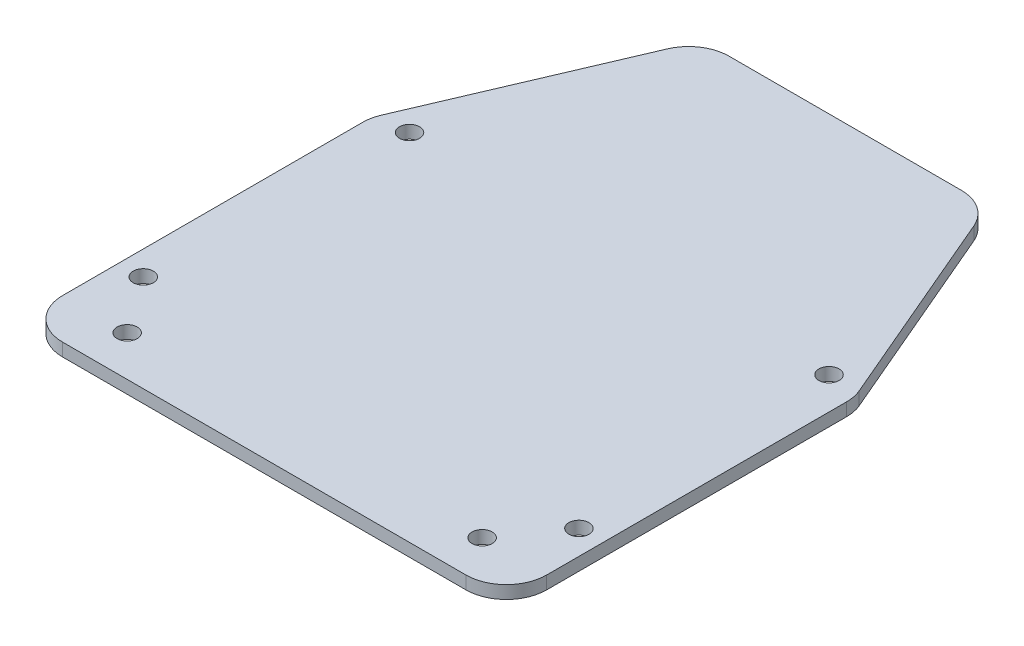
SolidWorks part; units mm, degrees
ref_plane "Front Plane" through (0, 0, 0) normal (0, 0, 1) x (1, 0, 0)
ref_plane "Top Plane" through (0, 0, 0) normal (0, 1, 0) x (1, 0, 0)
ref_plane "Right Plane" through (0, 0, 0) normal (1, 0, 0) x (0, 0, -1)
sketch "Sketch1" plane through (0, 0, 0) normal (0, 1, 0) x (1, 0, 0)
  line L0 (-17.7, 36) -> (-30, 7.2)
  line L1 (-30, -36) -> (30, -36)
  line L2 (-30, -36) -> (-30, 36)
  line L3 (-30, 36) -> (30, 36)
  line L4 (30, -36) -> (30, 36)
  line L5 (-30, -36) -> (30, 36) construction
  line L6 (-30, 36) -> (30, -36) construction
  line L7 (0, 0) -> (0, 36) construction
  line L8 (17.7, 36) -> (30, 7.2)
  point P0 (0, 0)
  dimension "D1" = 72
  dimension "D2" = 60
  dimension "D3" = 12.3
  dimension "D4" = 28.8
extrude "Boss-Extrude1" add sketch "Sketch1" along normal blind 1.6 contours L8 L3 L0 L2 L1 L4
sketch "Sketch2" plane through (0, 0, 0) normal (0, 1, 0) x (1, 0, 0)
  line L0 (30, -36) -> (30, 7.2) construction
  line L1 (-30, -36) -> (30, -36) construction
  line L2 (-30, -36) -> (-30, 7.2) construction
  circle A0 centre (-27, -24) radius 1.25
  circle A1 centre (27, -24) radius 1.25
  circle A2 centre (26, 8) radius 1.25
  circle A3 centre (-26, 8) radius 1.25
  circle A6 centre (-22, -31) radius 1.25
  circle A7 centre (22, -31) radius 1.25
  dimension "D1" = 4
  dimension "D2" = 3
  dimension "D3" = 12
  dimension "D4" = 32
  dimension "D5" = 3
  dimension "D7" = 2.5
  dimension "D8" = 8
  dimension "D6" = 4
  dimension "D9" = 5
  dimension "D10" = 8
extrude "Cut-Extrude1" cut sketch "Sketch2" against normal blind 2.5 from surface at 1.6 starting at face at (0, 1.6, -2.4)
fillet "Fillet1" radius 5 6 edges at (30, 0.8, -7.2) (30, 0.8, 36) (-30, 0.8, 36) (-30, 0.8, -7.2) (17.7, 0.8, -36) (-17.7, 0.8, -36)
